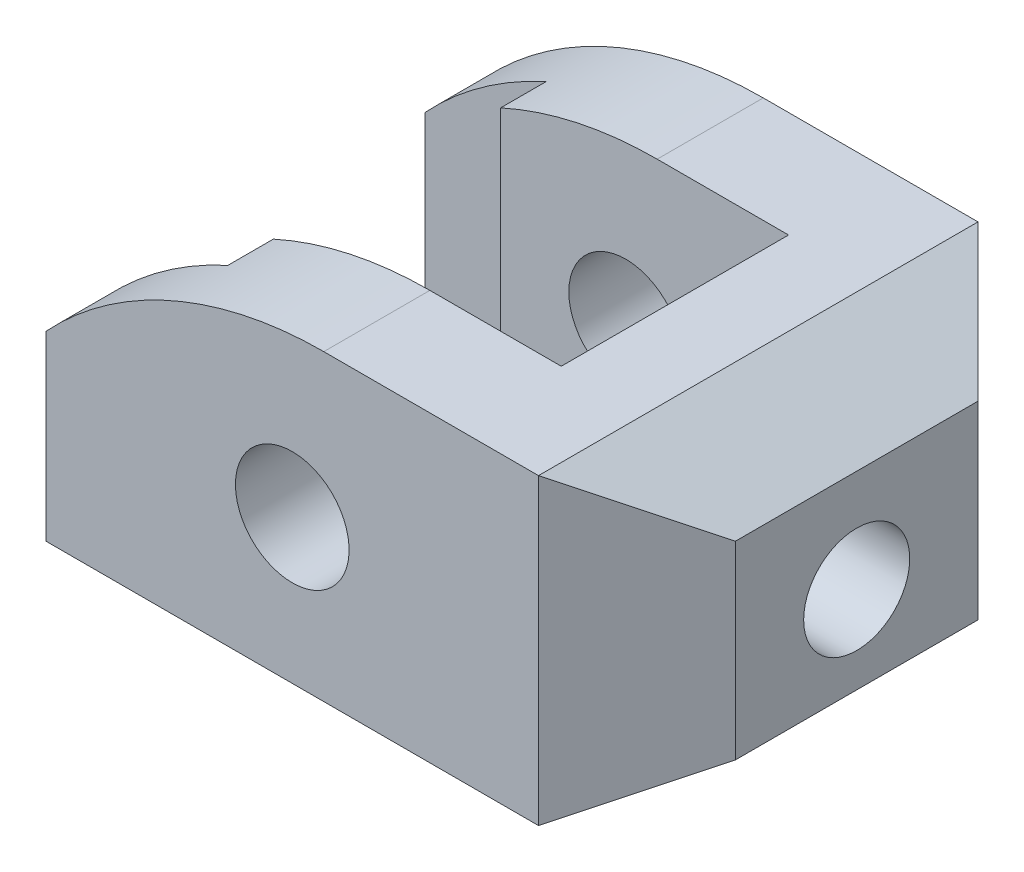
SolidWorks part; units mm, degrees
material "1060 Alloy"
ref_plane "Front Plane" through (0, 0, 0) normal (0, 0, 1) x (1, 0, 0)
ref_plane "Top Plane" through (0, 0, 0) normal (0, 1, 0) x (1, 0, 0)
ref_plane "Right Plane" through (0, 0, 0) normal (1, 0, 0) x (0, 0, -1)
sketch "Sketch1" plane through (0, 0, 0) normal (0, 0, 1) x (1, 0, 0)
  line L0 (0, 13.8138) -> (0, -28.7241) construction
  line L1 (32.5, -19) -> (-32.5, -19)
  line L2 (-32.5, -19) -> (-32.5, 5)
  line L3 (32.5, -19) -> (45.4904, -11.5)
  line L4 (45.4904, -11.5) -> (45.4904, 13.5)
  line L5 (45.4904, 13.5) -> (32.5, 21)
  line L6 (32.5, 21) -> (4.1606, 21)
  circle A0 centre (0, 0) radius 7.5
  arc A1 (-32.5, 5) -> (4.1606, 21) centre (4.1606, -29) cw
  point P8 (0, -19)
  dimension "D1" = 15
  dimension "D9" = 50
  dimension "D2" = 65
  dimension "D3" = 19
  dimension "D4" = 24
  dimension "D5" = 15
  dimension "D6" = 30
  dimension "D7" = 30
  dimension "D8" = 40
extrude "Boss-Extrude1" add sketch "Sketch1" along normal blind 58
sketch "Sketch2" plane through (0, 21, 0) normal (0, 1, 0) x (1, 0, 0)
  line L0 (45.4904, -29) -> (21.5, -29) construction
  line L1 (45.4904, -58) -> (45.4904, 0) construction
  line L2 (-32.5, -58) -> (-32.5, 0) construction
  line L3 (4.1606, -58) -> (4.1606, 0) construction
  line L4 (21.5, -44) -> (-16.5, -44)
  line L5 (21.5, -44) -> (21.5, -14)
  line L6 (21.5, -14) -> (-16.5, -14)
  line L7 (-16.5, -44) -> (-16.5, -14)
  line L8 (-16.5, -29) -> (-32.5, -29) construction
  line L9 (32.5, 0) -> (4.1606, 0) construction
  line L10 (32.5, -58) -> (32.5, 0) construction
  line L11 (32.5, -58) -> (4.1606, -58) construction
  point P6 (4.1606, -29)
  dimension "D1" = 11
  dimension "D2" = 16
  dimension "D3" = 14
  dimension "D4" = 14
extrude "Cut-Extrude1" cut sketch "Sketch2" against normal through all both and the other way through all
sketch "Sketch3" plane through (0, 21, 0) normal (0, 1, 0) x (1, 0, 0)
  line L0 (-32.5, -29) -> (45.4904, -29) construction
  line L1 (-32.5, -58) -> (-32.5, 0) construction
  line L2 (45.4904, -58) -> (45.4904, 0) construction
  line L3 (-16.5, -50) -> (-32.5, -50)
  line L4 (-16.5, -14) -> (-32.5, -14)
  line L5 (-16.5, -14) -> (-16.5, -8)
  line L6 (-16.5, -8) -> (-32.5, -8)
  line L7 (-32.5, -14) -> (-32.5, -8)
  line L8 (-32.5, -44) -> (-32.5, -50)
  line L9 (-16.5, -44) -> (-32.5, -44)
  line L10 (-16.5, -44) -> (-16.5, -50)
  dimension "D1" = 6
extrude "Cut-Extrude4" cut sketch "Sketch3" against normal through all both and the other way through all
sketch "Sketch4" plane through (45.4904, 0, 0) normal (1, 0, 0) x (0, 0, -1)
  line L0 (-58, -19) -> (0, -19) construction
  line L1 (-58, -11.5) -> (-58, 13.5) construction
  circle A0 centre (-29, 0) radius 7
  dimension "D1" = 14
  dimension "D2" = 19
  dimension "D3" = 29
extrude "Cut-Extrude5" cut sketch "Sketch4" against normal through all both and the other way through all
sketch "Sketch6" plane through (0, 21, 0) normal (0, 1, 0) x (1, 0, 0)
  line L0 (32.5, 0) -> (45.4904, -12.9904)
  line L1 (45.4904, -58) -> (45.4904, 0) construction
  line L2 (45.4904, -12.9904) -> (45.4904, 0)
  line L3 (45.4904, 0) -> (32.5, 0)
  line L4 (45.4904, -29) -> (32.5, -29) construction
  line L5 (32.5, -58) -> (32.5, 0) construction
  line L6 (45.4904, -45.0096) -> (45.4904, -58)
  line L7 (32.5, -58) -> (45.4904, -45.0096)
  line L8 (45.4904, -58) -> (32.5, -58)
  dimension "D1" = 45
extrude "Cut-Extrude6" cut sketch "Sketch6" against normal through all both and the other way through all
equation "\"A\"= 58mm"
equation "\"B\"= 40mm"
equation "\"C\"= 65mm"
equation "\"D2@Sketch1\"=\"C\""
equation "\"D8@Sketch1\"=\"B\""
equation "\"D3@Sketch4\"=\"A\"/2"
